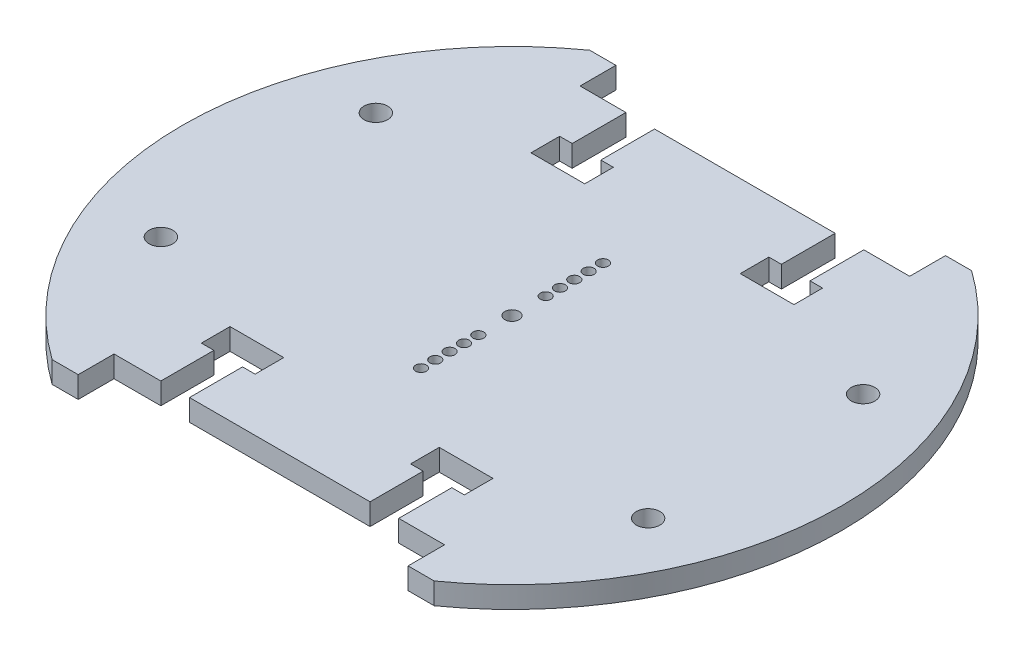
SolidWorks part; units mm, degrees
ref_plane "Front Plane" through (0, 0, 0) normal (0, 0, 1) x (1, 0, 0)
ref_plane "Top Plane" through (0, 0, 0) normal (0, 1, 0) x (1, 0, 0)
ref_plane "Right Plane" through (0, 0, 0) normal (1, 0, 0) x (0, 0, -1)
sketch "Sketch1" plane through (0, 0, 0) normal (0, 1, 0) x (1, 0, 0)
  line L0 (-26.6411, 37.5) -> (-23, 37.5)
  line L2 (-23, 37.5) -> (-23, 32.5)
  line L3 (23, 37.5) -> (23, 32.5)
  line L4 (-23, 32.5) -> (23, 32.5)
  line L5 (23, 37.5) -> (26.6411, 37.5)
  line L6 (0, 0) -> (-2.0728, 0) construction
  line L7 (23, -37.5) -> (26.6411, -37.5)
  line L8 (23, -37.5) -> (23, -32.4054)
  line L9 (-23.1326, -32.4054) -> (23, -32.4054)
  line L10 (-23.1326, -37.4054) -> (-23.1326, -32.4054)
  line L11 (-26.7738, -37.4054) -> (-23.1326, -37.4054)
  arc A1 (26.6411, -37.5) -> (26.6411, 37.5) centre (0, 0) ccw
  arc A7 (-26.7738, -37.4054) -> (-26.6411, 37.5) centre (0, 0) cw
  circle A12 centre (34, -15) radius 1.65
  circle A13 centre (34, 15) radius 1.65
  circle A14 centre (-34, 15) radius 1.65
  circle A15 centre (-34, -15) radius 1.65
  circle A16 centre (0, 0) radius 1
  circle A17 centre (0, 8.7) radius 0.75
  circle A18 centre (0, 10.7) radius 0.75
  circle A19 centre (0, 12.7) radius 0.75
  circle A20 centre (0, 6.7) radius 0.75
  circle A21 centre (0, 4.7) radius 0.75
  circle A22 centre (0, -12.7) radius 0.75
  circle A23 centre (0, -10.7) radius 0.75
  circle A24 centre (0, -8.7) radius 0.75
  circle A25 centre (0, -6.7) radius 0.75
  circle A26 centre (0, -4.7) radius 0.75
  point P5 (0, 32.5)
  dimension "D8" = 2
  dimension "D9" = 1.5
  dimension "D15" = 2
  dimension "D16" = 4.7
  dimension "D6" = 1.5
  dimension "D7" = 1.5
  dimension "D13" = 3.3
  dimension "D5" = 2
  dimension "D10" = 1.5
  dimension "D11" = 1.5
  dimension "D12" = 2
  dimension "D2" = 37.5
  dimension "D3" = 46
  dimension "D4" = 5
  dimension "D14" = 2
extrude "Boss-Extrude1" add sketch "Sketch1" along normal blind 3
sketch "Sketch2" plane through (0, 3, 0) normal (0, 1, 0) x (1, 0, 0)
  line L0 (23, 32.5) -> (-23, 32.5) construction
  line L1 (-16.6, 25) -> (-12.6, 25)
  line L2 (-16.6, 25) -> (-16.6, 32.5)
  line L3 (-16.6, 32.5) -> (-12.6, 32.5)
  line L4 (-12.6, 25) -> (-12.6, 32.5)
  line L5 (-16.6, 25) -> (-12.6, 32.5) construction
  line L6 (-16.6, 32.5) -> (-12.6, 25) construction
  line L7 (-23, 32.5) -> (-23, 37.5) construction
  line L8 (-18.35, 21) -> (-10.85, 21)
  line L9 (-18.35, 21) -> (-18.35, 25)
  line L10 (-18.35, 25) -> (-10.85, 25)
  line L11 (-10.85, 21) -> (-10.85, 25)
  line L12 (-18.35, 21) -> (-10.85, 25) construction
  line L13 (-18.35, 25) -> (-10.85, 21) construction
  line L14 (0, 0) -> (0, 25.8052) construction
  line L15 (0, 0) -> (-31.4227, 0) construction
  line L16 (18.35, 25) -> (10.85, 21) construction
  line L17 (18.35, 21) -> (10.85, 25) construction
  line L18 (16.6, 32.5) -> (12.6, 25) construction
  line L19 (16.6, 25) -> (12.6, 32.5) construction
  line L20 (10.85, 21) -> (10.85, 25)
  line L21 (18.35, 25) -> (10.85, 25)
  line L22 (18.35, 21) -> (18.35, 25)
  line L23 (18.35, 21) -> (10.85, 21)
  line L24 (12.6, 25) -> (12.6, 32.5)
  line L25 (16.6, 32.5) -> (12.6, 32.5)
  line L26 (16.6, 25) -> (16.6, 32.5)
  line L27 (16.6, 25) -> (12.6, 25)
  line L28 (16.6, -25) -> (12.6, -32.5) construction
  line L29 (16.6, -32.5) -> (12.6, -25) construction
  line L30 (18.35, -21) -> (10.85, -25) construction
  line L31 (18.35, -25) -> (10.85, -21) construction
  line L32 (-18.35, -25) -> (-10.85, -21) construction
  line L33 (-18.35, -21) -> (-10.85, -25) construction
  line L34 (-16.6, -32.5) -> (-12.6, -25) construction
  line L35 (-16.6, -25) -> (-12.6, -32.5) construction
  line L36 (16.6, -25) -> (12.6, -25)
  line L37 (16.6, -25) -> (16.6, -32.5)
  line L38 (16.6, -32.5) -> (12.6, -32.5)
  line L39 (12.6, -25) -> (12.6, -32.5)
  line L40 (18.35, -21) -> (10.85, -21)
  line L41 (18.35, -21) -> (18.35, -25)
  line L42 (18.35, -25) -> (10.85, -25)
  line L43 (10.85, -21) -> (10.85, -25)
  line L44 (-10.85, -21) -> (-10.85, -25)
  line L45 (-18.35, -25) -> (-10.85, -25)
  line L46 (-18.35, -21) -> (-18.35, -25)
  line L47 (-18.35, -21) -> (-10.85, -21)
  line L48 (-12.6, -25) -> (-12.6, -32.5)
  line L49 (-16.6, -32.5) -> (-12.6, -32.5)
  line L50 (-16.6, -25) -> (-16.6, -32.5)
  line L51 (-16.6, -25) -> (-12.6, -25)
  point P0 (-14.6, 28.75)
  point P7 (-14.6, 23)
  point P14 (-23, 35)
  point P27 (14.6, 23)
  point P28 (14.6, 28.75)
  point P45 (14.6, -28.75)
  point P46 (14.6, -23)
  point P47 (-14.6, -23)
  point P48 (-14.6, -28.75)
  line M12 (23, 32.5) -> (-23, 32.5)
  line M18 (-23.1326, -32.4054) -> (23, -32.4054)
  dimension "D1" = 6.4
  dimension "D2" = 4
  dimension "D3" = 7.5
  dimension "D4" = 4
  dimension "D5" = 7.5
extrude "Cut-Extrude1" cut sketch "Sketch2" against normal through all contours L1 L4 L2 M12 | L8 L11 L10 L1 L9 | L21 L26 L24 M12 | L23 L22 L21 L20 | L47 L46 L45 L44 | L45 L50 L48 M18 | L40 L43 L42 L36 L41 | L36 L39 L37 M18
